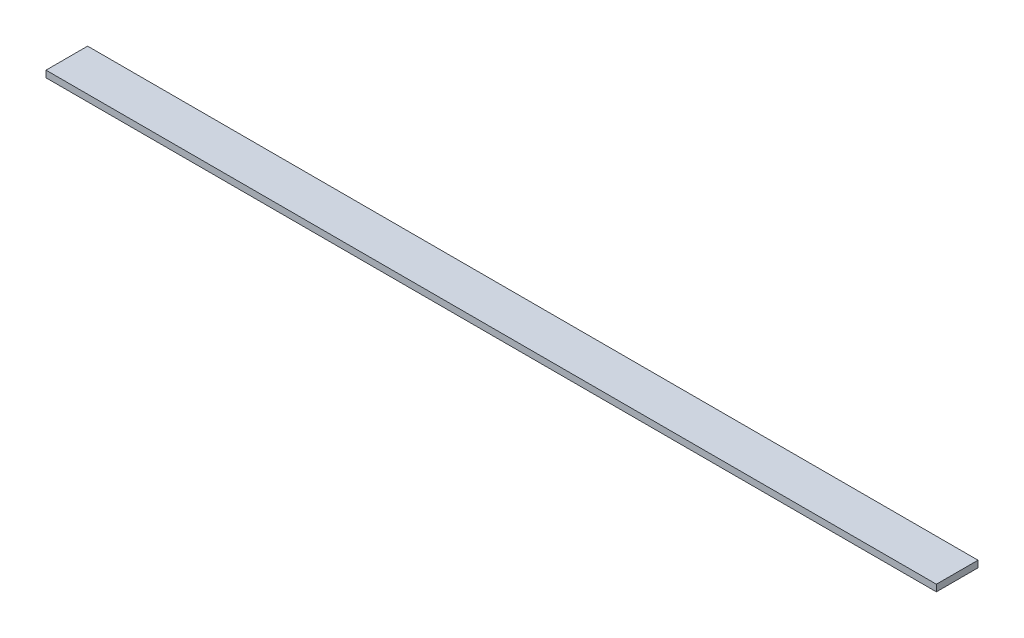
SolidWorks part; units mm, degrees
ref_plane "Спереди" through (0, 0, 0) normal (0, 0, 1) x (1, 0, 0)
ref_plane "Сверху" through (0, 0, 0) normal (0, 1, 0) x (1, 0, 0)
ref_plane "Справа" through (0, 0, 0) normal (1, 0, 0) x (0, 0, -1)
sketch "Эскиз1" plane through (0, 0, 0) normal (1, 0, 0) x (0, 0, -1)
  line L1 (-25, 0) -> (25, 0)
  line L2 (-25, 0) -> (-25, 8)
  line L3 (-25, 8) -> (25, 8)
  line L4 (25, 0) -> (25, 8)
  point P4 (0, 0)
extrude "Бобышка-Вытянуть1" add sketch "Эскиз1" along normal blind 1070
